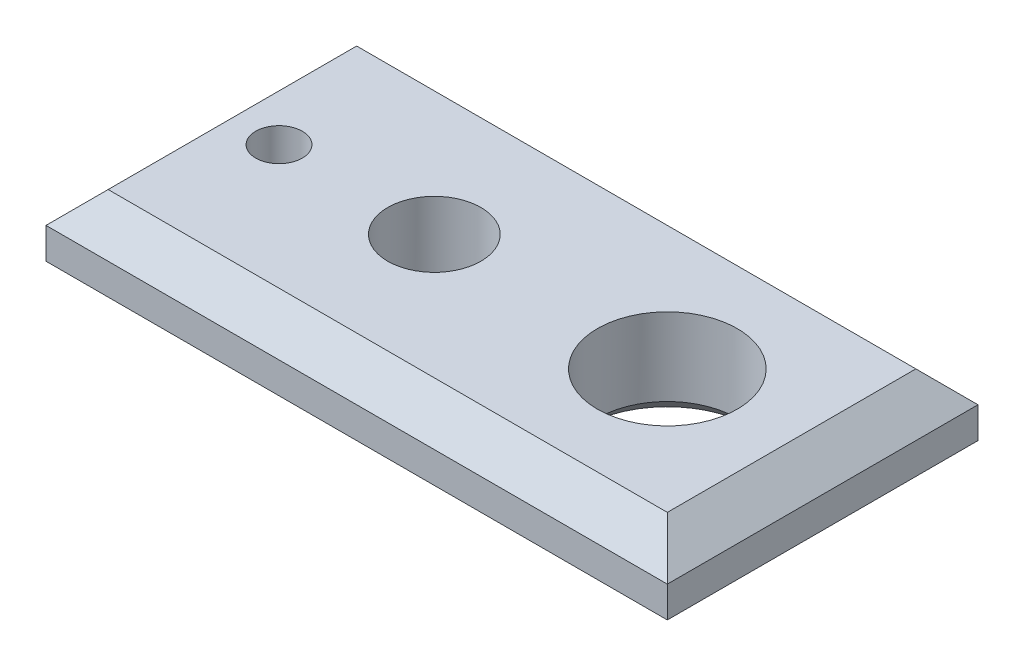
SolidWorks part; units mm, degrees
ref_plane "Alzado" through (0, 0, 0) normal (0, 0, 1) x (1, 0, 0)
ref_plane "Planta" through (0, 0, 0) normal (0, 1, 0) x (1, 0, 0)
ref_plane "Vista lateral" through (0, 0, 0) normal (1, 0, 0) x (0, 0, -1)
sketch "Croquis1" plane through (0, 0, 0) normal (0, 1, 0) x (1, 0, 0)
  line L1 (-100, -50) -> (100, -50)
  line L2 (-100, -50) -> (-100, 50)
  line L3 (-100, 50) -> (100, 50)
  line L4 (100, -50) -> (100, 50)
  line L5 (-100, -50) -> (100, 50) construction
  line L6 (-100, 50) -> (100, -50) construction
  point P0 (0, 0)
  dimension "D1" = 200
  dimension "D2" = 100
extrude "Saliente-Extruir1" add sketch "Croquis1" along normal blind 30
chamfer "Chaflán1" distance 10 angle 45 8 edges at (0, 0, -50) (-100, 0, 0) (0, 0, 50) (100, 0, 0) (0, 30, 50) (-100, 30, 0) (0, 30, -50) (100, 30, 0)
sketch "Croquis2" plane through (0, 30, 0) normal (0, 1, 0) x (1, 0, 0)
  line L0 (-100, -50) -> (-100, 50) construction
  circle A0 centre (-75, 0) radius 7.5
  circle A1 centre (-25, 0) radius 15
  circle A2 centre (50, 0) radius 22.5
  point P6 (0, 0)
  dimension "D4" = 15
  dimension "D5" = 30
  dimension "D6" = 45
  dimension "D1" = 25
  dimension "D2" = 50
  dimension "D3" = 75
extrude "Cortar-Extruir1" cut sketch "Croquis2" against normal up to next
chamfer "Chaflán3" distance 5 angle 45 3 edges at (50, 0, -22.5) (-25, 0, -15) (-75, 0, -7.5)
